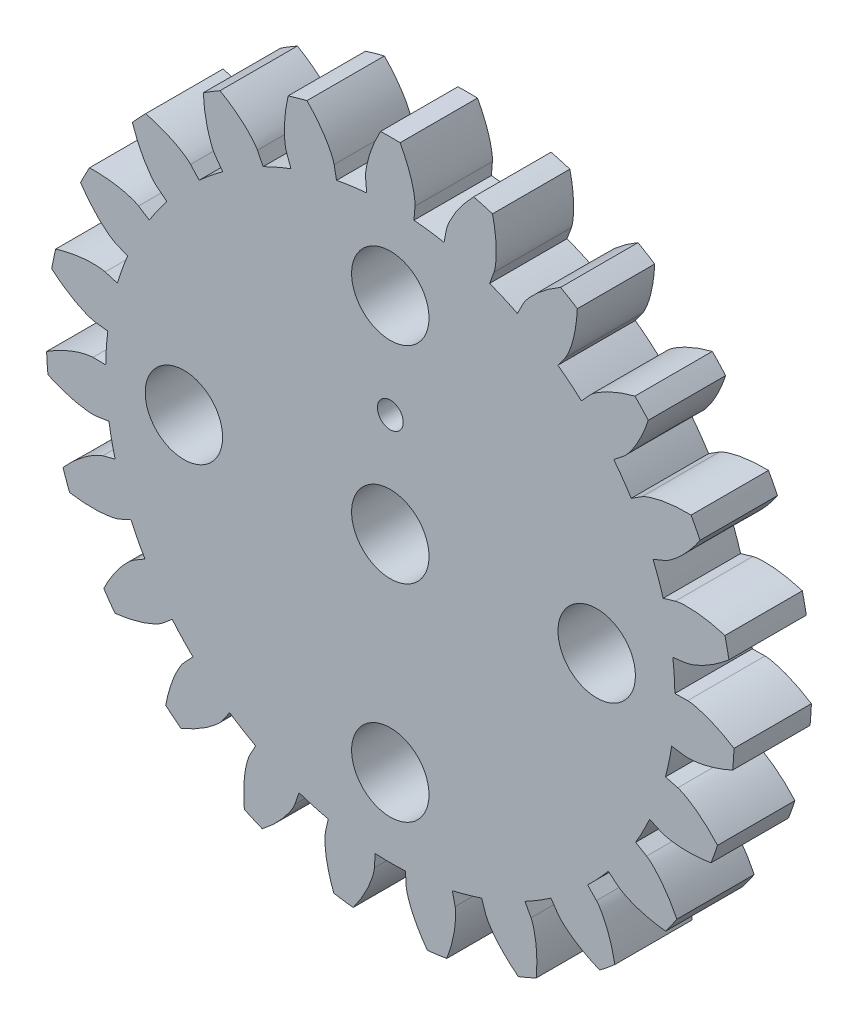
SolidWorks part; units mm, degrees
ref_plane "Front Plane" through (0, 0, 0) normal (0, 0, 1) x (1, 0, 0)
ref_plane "Top Plane" through (0, 0, 0) normal (0, 1, 0) x (1, 0, 0)
ref_plane "Right Plane" through (0, 0, 0) normal (1, 0, 0) x (0, 0, -1)
sketch "Model" plane through (0, 0, 0) normal (0, 0, 1) x (1, 0, 0)
  line L0 (-3.5387, -10.448) -> (-3.6973, -10.9162)
  line L1 (-5.4543, -10.153) -> (-5.2204, -9.7176)
  line L2 (-6.2264, -9.1058) -> (-6.5054, -9.5139)
  line L3 (-7.9913, -8.3049) -> (-7.6486, -7.9488)
  line L4 (-8.4522, -7.0883) -> (-8.8309, -7.4059)
  line L5 (-9.9356, -5.8409) -> (-9.5095, -5.5904)
  line L6 (-10.0512, -4.5451) -> (-10.5016, -4.7487)
  line L7 (-11.1431, -2.9437) -> (-10.6651, -2.8175)
  line L8 (-10.9047, -1.6648) -> (-11.3933, -1.7394)
  line L9 (-11.524, 0.1718) -> (-11.0298, 0.1644)
  line L10 (-10.9495, 1.339) -> (-11.4401, 1.399)
  line L11 (-11.0504, 3.2746) -> (-10.5764, 3.1341)
  line L12 (-10.1822, 4.2435) -> (-10.6384, 4.4336)
  line L13 (-9.7571, 6.1345) -> (-9.3387, 5.8714)
  line L14 (-8.6597, 6.8332) -> (-9.0477, 7.1394)
  line L15 (-7.7402, 8.5394) -> (-7.4083, 8.1732)
  line L16 (-6.495, 8.9162) -> (-6.786, 9.3157)
  line L17 (-5.1493, 10.3111) -> (-4.9285, 9.8688)
  line L18 (-3.8486, 10.3379) -> (-4.021, 10.8011)
  line L19 (-2.1765, 11.318) -> (-2.0831, 10.8326)
  line L20 (-0.9167, 10.9929) -> (-0.9578, 11.4855)
  line L21 (0.9578, 11.4855) -> (0.9167, 10.9929)
  line L22 (2.0831, 10.8326) -> (2.1765, 11.318)
  line L23 (4.021, 10.8011) -> (3.8486, 10.3379)
  line L24 (4.9285, 9.8688) -> (5.1493, 10.3111)
  line L25 (6.786, 9.3157) -> (6.495, 8.9162)
  line L26 (7.4083, 8.1732) -> (7.7402, 8.5394)
  line L27 (9.0477, 7.1394) -> (8.6597, 6.8332)
  line L28 (9.3387, 5.8714) -> (9.7571, 6.1345)
  line L29 (10.6384, 4.4336) -> (10.1822, 4.2435)
  line L30 (10.5764, 3.1341) -> (11.0504, 3.2746)
  line L31 (11.4401, 1.399) -> (10.9495, 1.339)
  line L32 (11.0298, 0.1644) -> (11.524, 0.1718)
  line L33 (11.3933, -1.7394) -> (10.9047, -1.6648)
  line L34 (10.6651, -2.8175) -> (11.1431, -2.9437)
  line L35 (10.5016, -4.7487) -> (10.0512, -4.5451)
  line L36 (9.5095, -5.5904) -> (9.9356, -5.8409)
  line L37 (8.8309, -7.4059) -> (8.4522, -7.0883)
  line L38 (7.6486, -7.9488) -> (7.9913, -8.3049)
  line L39 (6.5054, -9.5139) -> (6.2264, -9.1058)
  line L40 (5.2204, -9.7176) -> (5.4543, -10.153)
  line L41 (3.6973, -10.9162) -> (3.5387, -10.448)
  line L42 (2.405, -10.7657) -> (2.5128, -11.2481)
  line L43 (0.6151, -11.5089) -> (0.5887, -11.0153)
  line L44 (-0.5887, -11.0153) -> (-0.6151, -11.5089)
  line L45 (-2.5128, -11.2481) -> (-2.405, -10.7657)
  arc A0 (-5.6568, -12.0719) -> (-4.9615, -12.3739) centre (0, 0) ccw
  arc A1 (-6.2264, -9.1058) -> (-5.2204, -9.7176) centre (0, 0) ccw
  arc A2 (-8.704, -10.098) -> (-8.1159, -10.5765) centre (0, 0) ccw
  arc A3 (-8.4522, -7.0883) -> (-7.6486, -7.9488) centre (0, 0) ccw
  arc A4 (-11.1057, -7.3752) -> (-10.6684, -7.9946) centre (0, 0) ccw
  arc A5 (-10.0512, -4.5451) -> (-9.5095, -5.5904) centre (0, 0) ccw
  arc A6 (-12.6836, -4.1055) -> (-12.4297, -4.8198) centre (0, 0) ccw
  arc A7 (-10.9047, -1.6648) -> (-10.6651, -2.8175) centre (0, 0) ccw
  arc A8 (-13.3209, -0.5312) -> (-13.2692, -1.2876) centre (0, 0) ccw
  arc A9 (-10.9495, 1.339) -> (-11.0298, 0.1644) centre (0, 0) ccw
  arc A10 (-12.9703, 3.0824) -> (-13.1245, 2.3401) centre (0, 0) ccw
  arc A11 (-10.1822, 4.2435) -> (-10.5764, 3.1341) centre (0, 0) ccw
  arc A12 (-11.6577, 6.4675) -> (-12.0065, 5.7943) centre (0, 0) ccw
  arc A13 (-8.6597, 6.8332) -> (-9.3387, 5.8714) centre (0, 0) ccw
  arc A14 (-9.4805, 9.3728) -> (-9.998, 8.8187) centre (0, 0) ccw
  arc A15 (-6.495, 8.9162) -> (-7.4083, 8.1732) centre (0, 0) ccw
  arc A16 (-6.6002, 11.5831) -> (-7.2479, 11.1891) centre (0, 0) ccw
  arc A17 (-3.8486, 10.3379) -> (-4.9285, 9.8688) centre (0, 0) ccw
  arc A18 (-3.2303, 12.9342) -> (-3.9604, 12.7297) centre (0, 0) ccw
  arc A19 (-0.9167, 10.9929) -> (-2.0831, 10.8326) centre (0, 0) ccw
  arc A20 (0.3791, 13.3261) -> (-0.3791, 13.3261) centre (0, 0) ccw
  arc A21 (2.0831, 10.8326) -> (0.9167, 10.9929) centre (0, 0) ccw
  arc A22 (3.9604, 12.7297) -> (3.2303, 12.9342) centre (0, 0) ccw
  arc A23 (4.9285, 9.8688) -> (3.8486, 10.3379) centre (0, 0) ccw
  arc A24 (7.2479, 11.1891) -> (6.6002, 11.5831) centre (0, 0) ccw
  arc A25 (7.4083, 8.1732) -> (6.495, 8.9162) centre (0, 0) ccw
  arc A26 (9.998, 8.8187) -> (9.4805, 9.3728) centre (0, 0) ccw
  arc A27 (9.3387, 5.8714) -> (8.6597, 6.8332) centre (0, 0) ccw
  arc A28 (12.0065, 5.7943) -> (11.6577, 6.4675) centre (0, 0) ccw
  arc A29 (10.5764, 3.1341) -> (10.1822, 4.2435) centre (0, 0) ccw
  arc A30 (13.1245, 2.3401) -> (12.9703, 3.0824) centre (0, 0) ccw
  arc A31 (11.0298, 0.1644) -> (10.9495, 1.339) centre (0, 0) ccw
  arc A32 (13.2692, -1.2876) -> (13.3209, -0.5312) centre (0, 0) ccw
  arc A33 (10.6651, -2.8175) -> (10.9047, -1.6648) centre (0, 0) ccw
  arc A34 (12.4297, -4.8198) -> (12.6836, -4.1055) centre (0, 0) ccw
  arc A35 (9.5095, -5.5904) -> (10.0512, -4.5451) centre (0, 0) ccw
  arc A36 (10.6684, -7.9946) -> (11.1057, -7.3752) centre (0, 0) ccw
  arc A37 (7.6486, -7.9488) -> (8.4522, -7.0883) centre (0, 0) ccw
  arc A38 (8.1159, -10.5765) -> (8.704, -10.098) centre (0, 0) ccw
  arc A39 (5.2204, -9.7176) -> (6.2264, -9.1058) centre (0, 0) ccw
  arc A40 (4.9615, -12.3739) -> (5.6568, -12.0719) centre (0, 0) ccw
  arc A41 (2.405, -10.7657) -> (3.5387, -10.448) centre (0, 0) ccw
  arc A42 (1.439, -13.2536) -> (2.1901, -13.1504) centre (0, 0) ccw
  arc A43 (-0.5887, -11.0153) -> (0.5887, -11.0153) centre (0, 0) ccw
  arc A44 (-2.1901, -13.1504) -> (-1.439, -13.2536) centre (0, 0) ccw
  arc A45 (-3.5387, -10.448) -> (-2.405, -10.7657) centre (0, 0) ccw
  circle A46 centre (0, 0) radius 12.265 construction
  spline S0 degree 3 poles (-3.6973, -10.9162) (-3.7069, -10.9403) (-3.7475, -11.036) (-3.8652, -11.2386) (-4.0935, -11.5548) (-4.4634, -11.9567) (-4.7761, -12.2317) (-4.9615, -12.3739) knots 34.584629 34.584629 34.584629 34.584629 34.662509 34.896108 35.285436 35.830493 36.531279 36.531279 36.531279 36.531279
  spline S1 degree 3 poles (-5.6568, -12.0719) (-5.6795, -11.8394) (-5.6919, -11.4231) (-5.6506, -10.8784) (-5.5754, -10.4958) (-5.5076, -10.2714) (-5.4654, -10.1765) (-5.4543, -10.153) knots 37.289537 37.289537 37.289537 37.289537 37.990323 38.535379 38.924707 39.158307 39.236186 39.236186 39.236186 39.236186
  spline S2 degree 3 poles (-6.5054, -9.5139) (-6.5211, -9.5345) (-6.586, -9.6157) (-6.754, -9.779) (-7.0591, -10.0219) (-7.5237, -10.3091) (-7.8991, -10.4896) (-8.1159, -10.5765) knots 41.402696 41.402696 41.402696 41.402696 41.480575 41.714175 42.103503 42.648559 43.349345 43.349345 43.349345 43.349345
  spline S3 degree 3 poles (-8.704, -10.098) (-8.6631, -9.868) (-8.5627, -9.4638) (-8.376, -8.9505) (-8.2003, -8.6023) (-8.0746, -8.4046) (-8.0083, -8.3246) (-7.9913, -8.3049) knots 44.107603 44.107603 44.107603 44.107603 44.808389 45.353446 45.742774 45.976373 46.054253 46.054253 46.054253 46.054253
  spline S4 degree 3 poles (-8.8309, -7.4059) (-8.8517, -7.4216) (-8.936, -7.4822) (-9.1419, -7.5942) (-9.5012, -7.7457) (-10.0261, -7.8969) (-10.4362, -7.9695) (-10.6684, -7.9946) knots 48.220763 48.220763 48.220763 48.220763 48.298642 48.532242 48.921569 49.466626 50.167412 50.167412 50.167412 50.167412
  spline S5 degree 3 poles (-11.1057, -7.3752) (-11.0042, -7.1648) (-10.7985, -6.8027) (-10.4802, -6.3587) (-10.2171, -6.0709) (-10.0427, -5.9144) (-9.9573, -5.8552) (-9.9356, -5.8409) knots 50.92567 50.92567 50.92567 50.92567 51.626456 52.171513 52.56084 52.79444 52.87232 52.87232 52.87232 52.87232
  spline S6 degree 3 poles (-10.5016, -4.7487) (-10.5257, -4.7582) (-10.6233, -4.7938) (-10.8518, -4.8461) (-11.2386, -4.8951) (-11.7849, -4.8991) (-12.1993, -4.8583) (-12.4297, -4.8198) knots 55.038829 55.038829 55.038829 55.038829 55.116709 55.350309 55.739636 56.284693 56.985479 56.985479 56.985479 56.985479
  spline S7 degree 3 poles (-12.6836, -4.1055) (-12.5292, -3.9302) (-12.2334, -3.637) (-11.8072, -3.2954) (-11.4762, -3.0892) (-11.266, -2.9856) (-11.1678, -2.9517) (-11.1431, -2.9437) knots 57.743737 57.743737 57.743737 57.743737 58.444523 58.98958 59.378907 59.612507 59.690386 59.690386 59.690386 59.690386
  spline S8 degree 3 poles (-11.3933, -1.7394) (-11.4192, -1.7419) (-11.5228, -1.7499) (-11.7568, -1.7386) (-12.1426, -1.6814) (-12.6696, -1.5379) (-13.0577, -1.3868) (-13.2692, -1.2876) knots 61.856896 61.856896 61.856896 61.856896 61.934776 62.168375 62.557703 63.102759 63.803546 63.803546 63.803546 63.803546
  spline S9 degree 3 poles (-13.3209, -0.5312) (-13.1249, -0.4042) (-12.761, -0.2016) (-12.2584, 0.0123) (-11.8841, 0.1216) (-11.6537, 0.1646) (-11.55, 0.1708) (-11.524, 0.1718) knots 64.561804 64.561804 64.561804 64.561804 65.26259 65.807646 66.196974 66.430574 66.508453 66.508453 66.508453 66.508453
  spline S10 degree 3 poles (-11.4401, 1.399) (-11.4657, 1.4035) (-11.5676, 1.4238) (-11.7899, 1.4978) (-12.1459, 1.657) (-12.6147, 1.9374) (-12.9476, 2.1876) (-13.1245, 2.3401) knots 68.674963 68.674963 68.674963 68.674963 68.752842 68.986442 69.37577 69.920826 70.621612 70.621612 70.621612 70.621612
  spline S11 degree 3 poles (-12.9703, 3.0824) (-12.7472, 3.1519) (-12.3422, 3.2487) (-11.8005, 3.3192) (-11.4106, 3.3233) (-11.1772, 3.3026) (-11.0756, 3.2806) (-11.0504, 3.2746) knots 71.37987 71.37987 71.37987 71.37987 72.080656 72.625713 73.015041 73.24864 73.32652 73.32652 73.32652 73.32652
  spline S12 degree 3 poles (-10.6384, 4.4336) (-10.6618, 4.4449) (-10.7545, 4.4919) (-10.9486, 4.6231) (-11.2485, 4.8724) (-11.6242, 5.2689) (-11.8773, 5.5997) (-12.0065, 5.7943) knots 75.493029 75.493029 75.493029 75.493029 75.570909 75.804509 76.193836 76.738893 77.439679 77.439679 77.439679 77.439679
  spline S13 degree 3 poles (-11.6577, 6.4675) (-11.4242, 6.4742) (-11.008, 6.4581) (-10.4674, 6.3798) (-10.0908, 6.2786) (-9.8716, 6.1957) (-9.7798, 6.1471) (-9.7571, 6.1345) knots 78.197937 78.197937 78.197937 78.197937 78.898723 79.44378 79.833107 80.066707 80.144586 80.144586 80.144586 80.144586
  spline S14 degree 3 poles (-9.0477, 7.1394) (-9.0673, 7.1566) (-9.1438, 7.2268) (-9.2953, 7.4056) (-9.5168, 7.7266) (-9.7716, 8.2097) (-9.9261, 8.5965) (-9.998, 8.8187) knots 82.311096 82.311096 82.311096 82.311096 82.388976 82.622575 83.011903 83.55696 84.257746 84.257746 84.257746 84.257746
  spline S15 degree 3 poles (-9.4805, 9.3728) (-9.2538, 9.3163) (-8.8574, 9.1886) (-8.358, 8.9673) (-8.0227, 8.7683) (-7.834, 8.6293) (-7.7586, 8.5577) (-7.7402, 8.5394) knots 85.016004 85.016004 85.016004 85.016004 85.71679 86.261846 86.651174 86.884774 86.962653 86.962653 86.962653 86.962653
  spline S16 degree 3 poles (-6.786, 9.3157) (-6.8002, 9.3375) (-6.8549, 9.4258) (-6.9526, 9.6388) (-7.0793, 10.0076) (-7.1943, 10.5416) (-7.2387, 10.9557) (-7.2479, 11.1891) knots 89.129163 89.129163 89.129163 89.129163 89.207042 89.440642 89.82997 90.375026 91.075812 91.075812 91.075812 91.075812
  spline S17 degree 3 poles (-6.6002, 11.5831) (-6.3972, 11.4675) (-6.0499, 11.2375) (-5.6287, 10.8897) (-5.3595, 10.6076) (-5.2153, 10.4229) (-5.1621, 10.3337) (-5.1493, 10.3111) knots 91.83407 91.83407 91.83407 91.83407 92.534856 93.079913 93.469241 93.70284 93.78072 93.78072 93.78072 93.78072
  spline S18 degree 3 poles (-4.021, 10.8011) (-4.0288, 10.8259) (-4.0577, 10.9257) (-4.0943, 11.1572) (-4.1167, 11.5465) (-4.0834, 12.0917) (-4.0144, 12.5024) (-3.9604, 12.7297) knots 95.947229 95.947229 95.947229 95.947229 96.025109 96.258709 96.648036 97.193093 97.893879 97.893879 97.893879 97.893879
  spline S19 degree 3 poles (-3.2303, 12.9342) (-3.0661, 12.7682) (-2.7937, 12.4531) (-2.482, 12.0045) (-2.2989, 11.6602) (-2.2099, 11.4435) (-2.1827, 11.3432) (-2.1765, 11.318) knots 98.652137 98.652137 98.652137 98.652137 99.352923 99.89798 100.287307 100.520907 100.598787 100.598787 100.598787 100.598787
  spline S20 degree 3 poles (-0.9578, 11.4855) (-0.9586, 11.5114) (-0.9595, 11.6153) (-0.9323, 11.8481) (-0.8489, 12.229) (-0.6697, 12.745) (-0.4925, 13.1219) (-0.3791, 13.3261) knots 102.765296 102.765296 102.765296 102.765296 102.843176 103.076775 103.466103 104.01116 104.711946 104.711946 104.711946 104.711946
  spline S21 degree 3 poles (0.3791, 13.3261) (0.4925, 13.1219) (0.6697, 12.745) (0.8489, 12.229) (0.9323, 11.8481) (0.9595, 11.6153) (0.9586, 11.5114) (0.9578, 11.4855) knots 105.470204 105.470204 105.470204 105.470204 106.17099 106.716046 107.105374 107.338974 107.416853 107.416853 107.416853 107.416853
  spline S22 degree 3 poles (2.1765, 11.318) (2.1827, 11.3432) (2.2099, 11.4435) (2.2989, 11.6602) (2.482, 12.0045) (2.7937, 12.4531) (3.0661, 12.7682) (3.2303, 12.9342) knots 109.583363 109.583363 109.583363 109.583363 109.661242 109.894842 110.28417 110.829226 111.530012 111.530012 111.530012 111.530012
  spline S23 degree 3 poles (3.9604, 12.7297) (4.0144, 12.5024) (4.0834, 12.0917) (4.1167, 11.5465) (4.0943, 11.1572) (4.0577, 10.9257) (4.0288, 10.8259) (4.021, 10.8011) knots 112.28827 112.28827 112.28827 112.28827 112.989057 113.534113 113.923441 114.15704 114.23492 114.23492 114.23492 114.23492
  spline S24 degree 3 poles (5.1493, 10.3111) (5.1621, 10.3337) (5.2153, 10.4229) (5.3595, 10.6076) (5.6287, 10.8897) (6.0499, 11.2375) (6.3972, 11.4675) (6.6002, 11.5831) knots 116.40143 116.40143 116.40143 116.40143 116.479309 116.712909 117.102236 117.647293 118.348079 118.348079 118.348079 118.348079
  spline S25 degree 3 poles (7.2479, 11.1891) (7.2387, 10.9557) (7.1943, 10.5416) (7.0793, 10.0076) (6.9526, 9.6388) (6.8549, 9.4258) (6.8002, 9.3375) (6.786, 9.3157) knots 119.106337 119.106337 119.106337 119.106337 119.807123 120.35218 120.741507 120.975107 121.052987 121.052987 121.052987 121.052987
  spline S26 degree 3 poles (7.7402, 8.5394) (7.7586, 8.5577) (7.834, 8.6293) (8.0227, 8.7683) (8.358, 8.9673) (8.8574, 9.1886) (9.2538, 9.3163) (9.4805, 9.3728) knots 123.219496 123.219496 123.219496 123.219496 123.297376 123.530976 123.920303 124.46536 125.166146 125.166146 125.166146 125.166146
  spline S27 degree 3 poles (9.998, 8.8187) (9.9261, 8.5965) (9.7716, 8.2097) (9.5168, 7.7266) (9.2953, 7.4056) (9.1438, 7.2268) (9.0673, 7.1566) (9.0477, 7.1394) knots 125.924404 125.924404 125.924404 125.924404 126.62519 127.170247 127.559574 127.793174 127.871053 127.871053 127.871053 127.871053
  spline S28 degree 3 poles (9.7571, 6.1345) (9.7798, 6.1471) (9.8716, 6.1957) (10.0908, 6.2786) (10.4674, 6.3798) (11.008, 6.4581) (11.4242, 6.4742) (11.6577, 6.4675) knots 130.037563 130.037563 130.037563 130.037563 130.115443 130.349042 130.73837 131.283426 131.984213 131.984213 131.984213 131.984213
  spline S29 degree 3 poles (12.0065, 5.7943) (11.8773, 5.5997) (11.6242, 5.2689) (11.2485, 4.8724) (10.9486, 4.6231) (10.7545, 4.4919) (10.6618, 4.4449) (10.6384, 4.4336) knots 132.742471 132.742471 132.742471 132.742471 133.443257 133.988313 134.377641 134.611241 134.68912 134.68912 134.68912 134.68912
  spline S30 degree 3 poles (11.0504, 3.2746) (11.0756, 3.2806) (11.1772, 3.3026) (11.4106, 3.3233) (11.8005, 3.3192) (12.3422, 3.2487) (12.7472, 3.1519) (12.9703, 3.0824) knots 136.85563 136.85563 136.85563 136.85563 136.933509 137.167109 137.556437 138.101493 138.802279 138.802279 138.802279 138.802279
  spline S31 degree 3 poles (13.1245, 2.3401) (12.9476, 2.1876) (12.6147, 1.9374) (12.1459, 1.657) (11.7899, 1.4978) (11.5676, 1.4238) (11.4657, 1.4035) (11.4401, 1.399) knots 139.560537 139.560537 139.560537 139.560537 140.261323 140.80638 141.195708 141.429307 141.507187 141.507187 141.507187 141.507187
  spline S32 degree 3 poles (11.524, 0.1718) (11.55, 0.1708) (11.6537, 0.1646) (11.8841, 0.1216) (12.2584, 0.0123) (12.761, -0.2016) (13.1249, -0.4042) (13.3209, -0.5312) knots 143.673696 143.673696 143.673696 143.673696 143.751576 143.985176 144.374503 144.91956 145.620346 145.620346 145.620346 145.620346
  spline S33 degree 3 poles (13.2692, -1.2876) (13.0577, -1.3868) (12.6696, -1.5379) (12.1426, -1.6814) (11.7568, -1.7386) (11.5228, -1.7499) (11.4192, -1.7419) (11.3933, -1.7394) knots 146.378604 146.378604 146.378604 146.378604 147.07939 147.624447 148.013774 148.247374 148.325254 148.325254 148.325254 148.325254
  spline S34 degree 3 poles (11.1431, -2.9437) (11.1678, -2.9517) (11.266, -2.9856) (11.4762, -3.0892) (11.8072, -3.2954) (12.2334, -3.637) (12.5292, -3.9302) (12.6836, -4.1055) knots 150.491763 150.491763 150.491763 150.491763 150.569643 150.803242 151.19257 151.737627 152.438413 152.438413 152.438413 152.438413
  spline S35 degree 3 poles (12.4297, -4.8198) (12.1993, -4.8583) (11.7849, -4.8991) (11.2386, -4.8951) (10.8518, -4.8461) (10.6233, -4.7938) (10.5257, -4.7582) (10.5016, -4.7487) knots 153.196671 153.196671 153.196671 153.196671 153.897457 154.442513 154.831841 155.065441 155.14332 155.14332 155.14332 155.14332
  spline S36 degree 3 poles (9.9356, -5.8409) (9.9573, -5.8552) (10.0427, -5.9144) (10.2171, -6.0709) (10.4802, -6.3587) (10.7985, -6.8027) (11.0042, -7.1648) (11.1057, -7.3752) knots 157.30983 157.30983 157.30983 157.30983 157.387709 157.621309 158.010637 158.555693 159.256479 159.256479 159.256479 159.256479
  spline S37 degree 3 poles (10.6684, -7.9946) (10.4362, -7.9695) (10.0261, -7.8969) (9.5012, -7.7457) (9.1419, -7.5942) (8.936, -7.4822) (8.8517, -7.4216) (8.8309, -7.4059) knots 160.014737 160.014737 160.014737 160.014737 160.715523 161.26058 161.649908 161.883507 161.961387 161.961387 161.961387 161.961387
  spline S38 degree 3 poles (7.9913, -8.3049) (8.0083, -8.3246) (8.0746, -8.4046) (8.2003, -8.6023) (8.376, -8.9505) (8.5627, -9.4638) (8.6631, -9.868) (8.704, -10.098) knots 164.127897 164.127897 164.127897 164.127897 164.205776 164.439376 164.828703 165.37376 166.074546 166.074546 166.074546 166.074546
  spline S39 degree 3 poles (8.1159, -10.5765) (7.8991, -10.4896) (7.5237, -10.3091) (7.0591, -10.0219) (6.754, -9.779) (6.586, -9.6157) (6.5211, -9.5345) (6.5054, -9.5139) knots 166.832804 166.832804 166.832804 166.832804 167.53359 168.078647 168.467974 168.701574 168.779454 168.779454 168.779454 168.779454
  spline S40 degree 3 poles (5.4543, -10.153) (5.4654, -10.1765) (5.5076, -10.2714) (5.5754, -10.4958) (5.6506, -10.8784) (5.6919, -11.4231) (5.6795, -11.8394) (5.6568, -12.0719) knots 170.945963 170.945963 170.945963 170.945963 171.023843 171.257442 171.64677 172.191827 172.892613 172.892613 172.892613 172.892613
  spline S41 degree 3 poles (4.9615, -12.3739) (4.7761, -12.2317) (4.4634, -11.9567) (4.0935, -11.5548) (3.8652, -11.2386) (3.7475, -11.036) (3.7069, -10.9403) (3.6973, -10.9162) knots 173.650871 173.650871 173.650871 173.650871 174.351657 174.896713 175.286041 175.519641 175.59752 175.59752 175.59752 175.59752
  spline S42 degree 3 poles (2.5128, -11.2481) (2.5172, -11.2737) (2.5322, -11.3765) (2.5369, -11.6108) (2.5061, -11.9995) (2.3989, -12.5351) (2.2746, -12.9326) (2.1901, -13.1504) knots 177.76403 177.76403 177.76403 177.76403 177.841909 178.075509 178.464837 179.009893 179.710679 179.710679 179.710679 179.710679
  spline S43 degree 3 poles (1.439, -13.2536) (1.2989, -13.0667) (1.072, -12.7175) (0.8242, -12.2307) (0.6897, -11.8647) (0.6311, -11.6378) (0.6178, -11.5347) (0.6151, -11.5089) knots 180.468937 180.468937 180.468937 180.468937 181.169724 181.71478 182.104108 182.337707 182.415587 182.415587 182.415587 182.415587
  spline S44 degree 3 poles (-0.6151, -11.5089) (-0.6178, -11.5347) (-0.6311, -11.6378) (-0.6897, -11.8647) (-0.8242, -12.2307) (-1.072, -12.7175) (-1.2989, -13.0667) (-1.439, -13.2536) knots 184.582097 184.582097 184.582097 184.582097 184.659976 184.893576 185.282903 185.82796 186.528746 186.528746 186.528746 186.528746
  spline S45 degree 3 poles (-2.1901, -13.1504) (-2.2746, -12.9326) (-2.3989, -12.5351) (-2.5061, -11.9995) (-2.5369, -11.6108) (-2.5322, -11.3765) (-2.5172, -11.2737) (-2.5128, -11.2481) knots 187.287004 187.287004 187.287004 187.287004 187.98779 188.532847 188.922174 189.155774 189.233654 189.233654 189.233654 189.233654
extrude "Boss-Extrude1" add sketch "Model" along normal blind 3
sketch "Sketch2" plane through (0, 0, 0) normal (0, 0, 1) x (1, 0, 0)
  line L0 (0, 8) -> (0, 0) construction
  circle A0 centre (0, 0) radius 1.5
  circle A1 centre (0, 0) radius 8 construction
  circle A2 centre (0, 8) radius 1.5
  circle A3 centre (-8, 0) radius 1.5
  circle A4 centre (0, -8) radius 1.5
  circle A5 centre (8, 0) radius 1.5
  circle A6 centre (0, 4) radius 0.5
  dimension "D1" = 3
  dimension "D2" = 16
  dimension "D3" = 3
  dimension "D4" = 1
extrude "Cut-Extrude1" cut sketch "Sketch2" along normal through all
